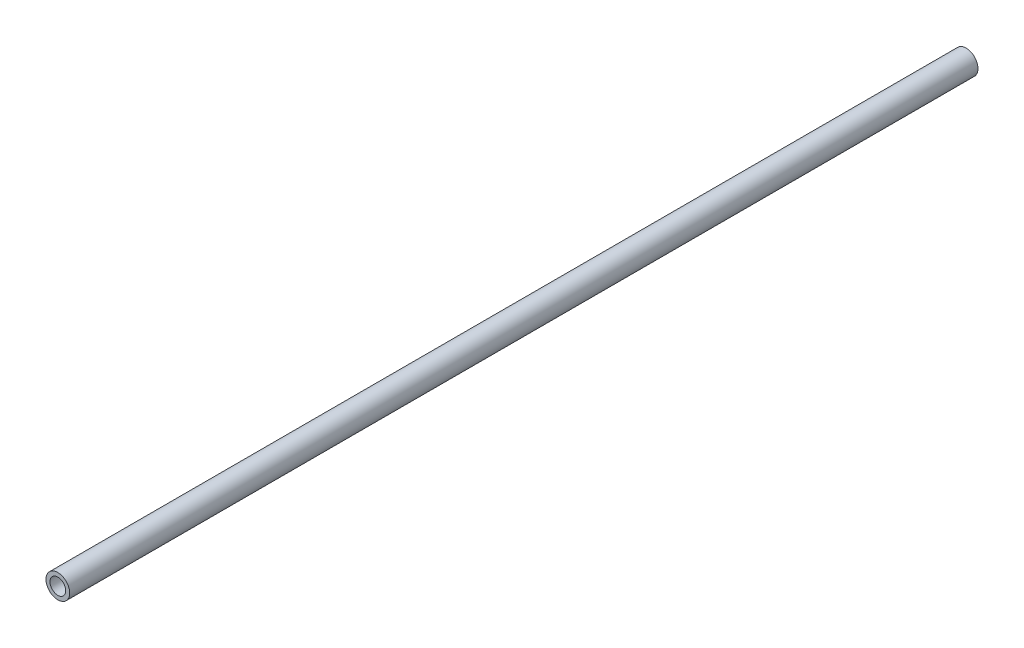
SolidWorks part; units mm, degrees
material "PVC Rigid"
ref_plane "Front Plane" through (0, 0, 0) normal (0, 0, 1) x (1, 0, 0)
ref_plane "Top Plane" through (0, 0, 0) normal (0, 1, 0) x (1, 0, 0)
ref_plane "Right Plane" through (0, 0, 0) normal (1, 0, 0) x (0, 0, -1)
sketch "Sketch1" plane through (0, 0, 0) normal (0, 0, 1) x (1, 0, 0)
  circle A0 centre (0, 0) radius 7.62
  circle A2 centre (0, 0) radius 5.08
  dimension "D1" = 15.24
  dimension "D2" = 10.16
extrude "Boss-Extrude1" add sketch "Sketch1" along normal blind 584.2
